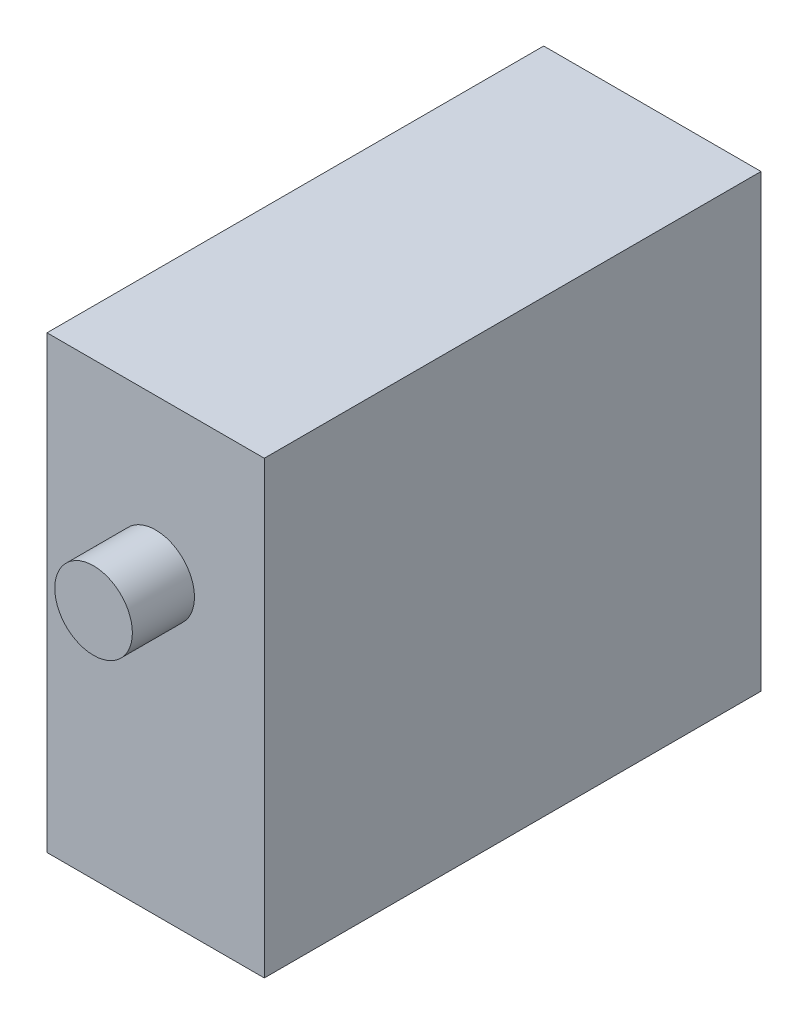
SolidWorks part; units mm, degrees
ref_plane "Front Plane" through (0, 0, 0) normal (0, 0, 1) x (1, 0, 0)
ref_plane "Top Plane" through (0, 0, 0) normal (0, 1, 0) x (1, 0, 0)
ref_plane "Right Plane" through (0, 0, 0) normal (1, 0, 0) x (0, 0, -1)
sketch "Sketch1" plane through (0, 0, 0) normal (0, 0, 1) x (1, 0, 0)
  line L1 (7, 14.5) -> (-7, 14.5)
  line L2 (7, 14.5) -> (7, -14.5)
  line L3 (7, -14.5) -> (-7, -14.5)
  line L4 (-7, 14.5) -> (-7, -14.5)
  line L5 (7, 14.5) -> (-7, -14.5) construction
  line L6 (7, -14.5) -> (-7, 14.5) construction
  point P0 (0, 0)
  dimension "D1" = 29
  dimension "D2" = 14
extrude "Boss-Extrude1" add sketch "Sketch1" along normal blind 32
sketch "Sketch2" plane through (0, 0, 32) normal (0, 0, 1) x (1, 0, 0)
  line L0 (0, 0) -> (0, 50000) construction
  line L1 (7, 14.5) -> (-7, 14.5) construction
  circle A0 centre (0, 4.5) radius 2.5
  dimension "D1" = 5
  dimension "D2" = 10
extrude "Boss-Extrude2" add sketch "Sketch2" along normal blind 4
